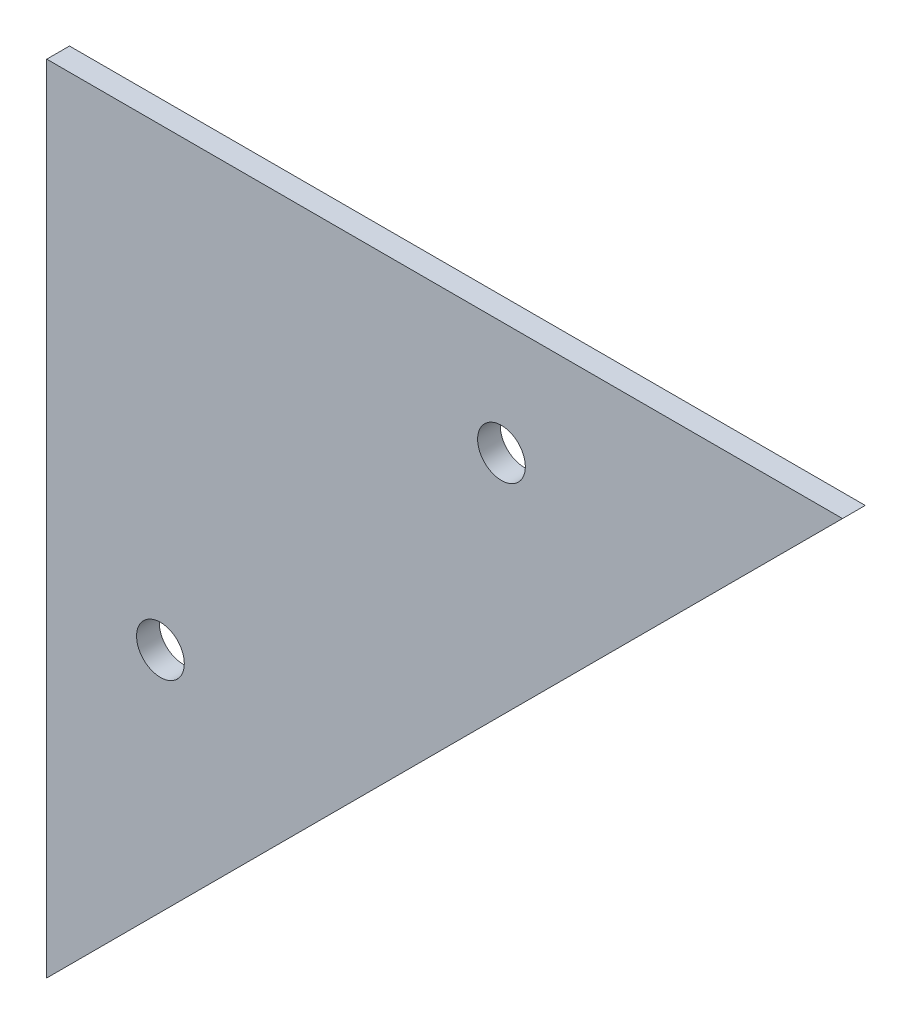
SolidWorks part; units mm, degrees
ref_plane "正面" through (0, 0, 0) normal (0, 0, 1) x (1, 0, 0)
ref_plane "平面" through (0, 0, 0) normal (0, 1, 0) x (1, 0, 0)
ref_plane "右側面" through (0, 0, 0) normal (1, 0, 0) x (0, 0, -1)
sketch "ｽｹｯﾁ1" plane through (0, 0, 0) normal (0, 0, 1) x (1, 0, 0)
  line L0 (0, 0) -> (0, -70)
  line L1 (0, -70) -> (70, 0)
  line L2 (70, 0) -> (0, 0)
  line L3 (10, -10) -> (10, -40)
  line L4 (0, 0) -> (10, 0)
  line L5 (0, 0) -> (0, -10)
  line L6 (0, -10) -> (10, -10)
  line L7 (10, 0) -> (10, -10)
  line L8 (10, -10) -> (40, -10)
  circle A0 centre (10, -40) radius 2.1
  circle A1 centre (40, -10) radius 2.1
  dimension "D7" = 4.2
  dimension "D8" = 4.2
  dimension "D1" = 70
  dimension "D2" = 70
  dimension "D3" = 10
  dimension "D4" = 10
  dimension "D5" = 30
  dimension "D6" = 30
extrude "ﾎﾞｽ - 押し出し1" add sketch "ｽｹｯﾁ1" along normal blind 2
